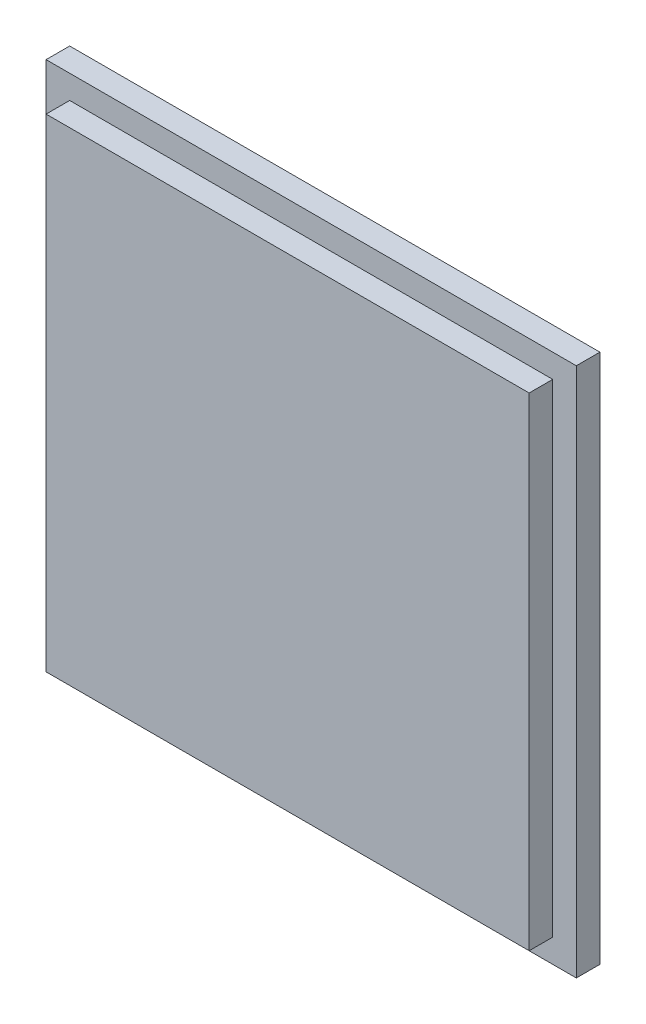
SolidWorks part; units mm, degrees
ref_plane "Front Plane" through (0, 0, 0) normal (0, 0, 1) x (1, 0, 0)
ref_plane "Top Plane" through (0, 0, 0) normal (0, 1, 0) x (1, 0, 0)
ref_plane "Right Plane" through (0, 0, 0) normal (1, 0, 0) x (0, 0, -1)
sketch "Sketch2" plane through (0, 0, 0) normal (0, 0, 1) x (1, 0, 0)
  line L1 (-28.1, -28.1) -> (28.1, -28.1)
  line L2 (-28.1, -28.1) -> (-28.1, 28.1)
  line L3 (-28.1, 28.1) -> (28.1, 28.1)
  line L4 (28.1, -28.1) -> (28.1, 28.1)
  line L5 (-28.1, -28.1) -> (28.1, 28.1) construction
  line L6 (-28.1, 28.1) -> (28.1, -28.1) construction
  point P0 (0, 0)
extrude "Boss-Extrude1" add sketch "Sketch2" along normal blind 2.5
sketch "Sketch3" plane through (0, 0, 2.5) normal (0, 0, 1) x (1, 0, 0)
  line L1 (-25.6, -25.6) -> (25.6, -25.6)
  line L2 (-25.6, -25.6) -> (-25.6, 25.6)
  line L3 (-25.6, 25.6) -> (25.6, 25.6)
  line L4 (25.6, -25.6) -> (25.6, 25.6)
  line L5 (-25.6, -25.6) -> (25.6, 25.6) construction
  line L6 (-25.6, 25.6) -> (25.6, -25.6) construction
  point P0 (0, 0)
extrude "Boss-Extrude2" add sketch "Sketch3" along normal blind 2.5
